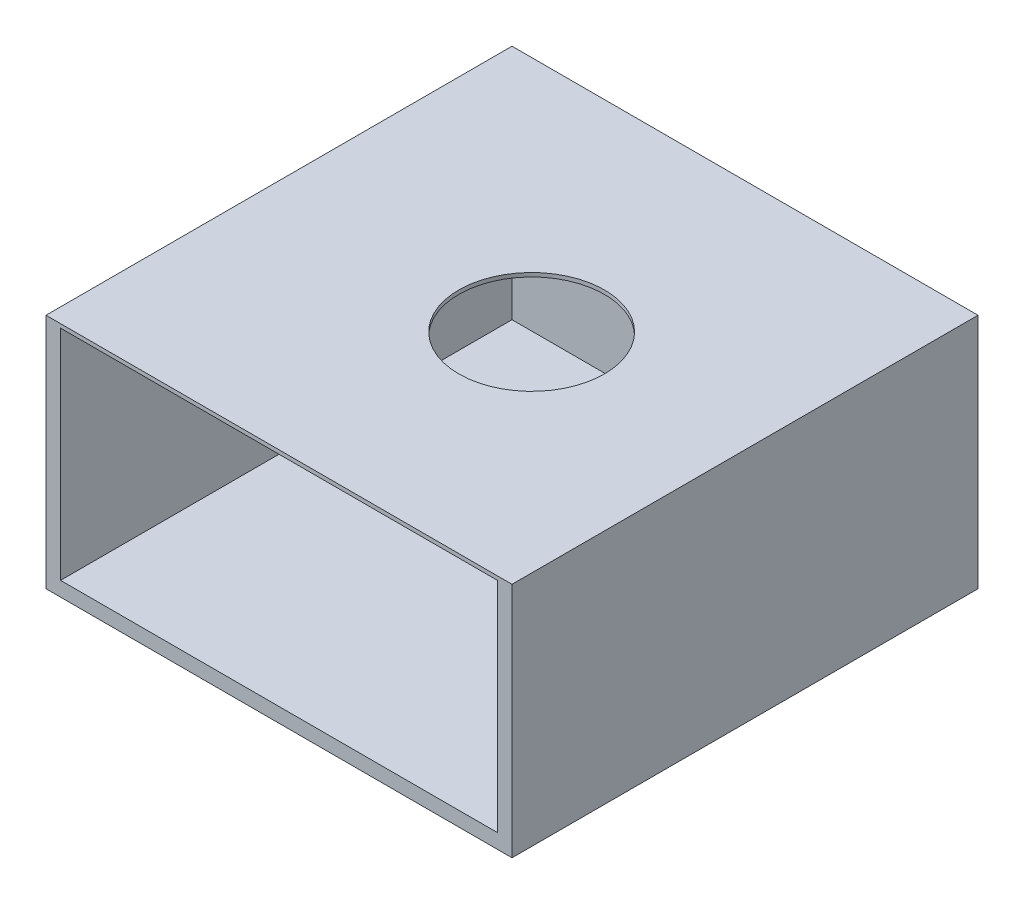
SolidWorks part; units mm, degrees
ref_plane "Front Plane" through (0, 0, 0) normal (0, 0, 1) x (1, 0, 0)
ref_plane "Top Plane" through (0, 0, 0) normal (0, 1, 0) x (1, 0, 0)
ref_plane "Right Plane" through (0, 0, 0) normal (1, 0, 0) x (0, 0, -1)
sketch "Sketch1" plane through (0, 0, 0) normal (0, 0, 1) x (1, 0, 0)
  line L1 (-152.4, -76.2) -> (152.4, -76.2)
  line L2 (-152.4, -76.2) -> (-152.4, 76.2)
  line L3 (-152.4, 76.2) -> (152.4, 76.2)
  line L4 (152.4, -76.2) -> (152.4, 76.2)
  line L5 (-152.4, -76.2) -> (152.4, 76.2) construction
  line L6 (-152.4, 76.2) -> (152.4, -76.2) construction
  point P0 (0, 0)
  dimension "D1" = 304.8
  dimension "D2" = 152.4
extrude "Boss-Extrude1" add sketch "Sketch1" along normal blind 304.8
shell "Shell1" thickness 9.525
sketch "Sketch2" plane through (0, 76.2, 0) normal (0, 1, 0) x (1, 0, 0)
  line L0 (-142.875, -304.8) -> (142.875, -304.8)
  line L8 (-152.4, -304.8) -> (-142.875, -304.8)
  line L9 (-142.875, -304.8) -> (-142.875, -9.525)
  line L10 (-142.875, -9.525) -> (142.875, -9.525)
  line L11 (142.875, -9.525) -> (142.875, -304.8)
  line L12 (142.875, -304.8) -> (152.4, -304.8)
  line L13 (152.4, -304.8) -> (152.4, 0)
  line L14 (152.4, 0) -> (-152.4, 0)
  line L15 (-152.4, 0) -> (-152.4, -304.8)
  line L16 (-152.4, -304.8) -> (-142.875, -304.8)
  line L20 (142.875, -304.8) -> (152.4, -304.8)
  line L21 (152.4, -304.8) -> (152.4, 0)
  line L22 (152.4, 0) -> (-152.4, 0)
  line L23 (-152.4, 0) -> (-152.4, -304.8)
  dimension "D1" = 0
extrude "Boss-Extrude2" add sketch "Sketch2" along normal blind 2.54
sketch "Sketch3" plane through (0, 78.74, 0) normal (0, 1, 0) x (1, 0, 0)
  line L10 (15.875, -108.3347) -> (-28.9142, -140.876)
  line L11 (-28.9142, -140.876) -> (-11.8063, -193.5289)
  line L12 (-11.8063, -193.5289) -> (43.5563, -193.5289)
  line L13 (43.5563, -193.5289) -> (60.6642, -140.876)
  line L14 (60.6642, -140.876) -> (15.875, -108.3347)
  circle A1 centre (15.875, -155.4289) radius 3.175
sketch "Sketch4" plane through (0, 78.74, 0) normal (0, 1, 0) x (1, 0, 0)
  circle A1 centre (15.875, -155.4289) radius 47.625
  point P2 (0, 0)
  dimension "D1" = 95.25
  dimension "D2" = 0
extrude "Cut-Extrude1" cut sketch "Sketch4" against normal blind 7.62
sketch "Sketch5" plane through (0, 78.74, 0) normal (0, 1, 0) x (1, 0, 0)
  line L2 (89.7396, -162.406) -> (138.9776, -162.406)
  line L3 (138.9776, -156.056) -> (89.7396, -156.056)
  ellipse E1 centre (138.9776, -159.231) end of major axis (138.9776, -156.056) minor radius 3.0047
sketch "Sketch6" plane through (0, 78.74, 0) normal (0, 1, 0) x (1, 0, 0)
  line L0 (138.9776, -159.231) -> (95.0898, -159.231) construction
  line L1 (138.9776, -163.5234) -> (95.0898, -163.5234)
  line L2 (138.9776, -154.9386) -> (95.0898, -154.9386)
  arc A0 (138.9776, -163.5234) -> (138.9776, -154.9386) centre (138.9776, -159.231) ccw
  arc A1 (95.0898, -154.9386) -> (95.0898, -163.5234) centre (95.0898, -159.231) ccw
  point P3 (117.0337, -159.231)
extrude "Cut-Extrude2" [suppressed] cut sketch "Sketch6" against normal blind 2.54
sketch "Sketch8" plane through (0, 78.74, 0) normal (0, 1, 0) x (1, 0, 0)
  line L1 (138.4375, -185.3651) -> (89.5629, -185.3651)
  line L4 (-152.4, 0) -> (-152.4, -304.8)
  line L5 (-152.4, -304.8) -> (152.4, -304.8)
  line L6 (152.4, -304.8) -> (152.4, 0)
  line L7 (152.4, 0) -> (-152.4, 0)
  line L8 (-152.4, 0) -> (-152.4, -304.8)
  line L9 (-152.4, -304.8) -> (152.4, -304.8)
  line L10 (152.4, -304.8) -> (152.4, 0)
  line L11 (152.4, 0) -> (-152.4, 0)
  ellipse E2 centre (138.4375, -188.5401) end of major axis (138.4375, -185.3651) minor radius 3.0073
  dimension "D1" = 0
sketch "Sketch9" plane through (0, 78.74, 0) normal (0, 1, 0) x (1, 0, 0)
  line L0 (138.4375, -188.5401) -> (91.5808, -188.5401) construction
  line L1 (138.4375, -194.05) -> (91.5808, -194.05)
  line L2 (138.4375, -183.0302) -> (91.5808, -183.0302)
  arc A0 (138.4375, -194.05) -> (138.4375, -183.0302) centre (138.4375, -188.5401) ccw
  arc A1 (91.5808, -183.0302) -> (91.5808, -194.05) centre (91.5808, -188.5401) ccw
  point P3 (115.0091, -188.5401)
